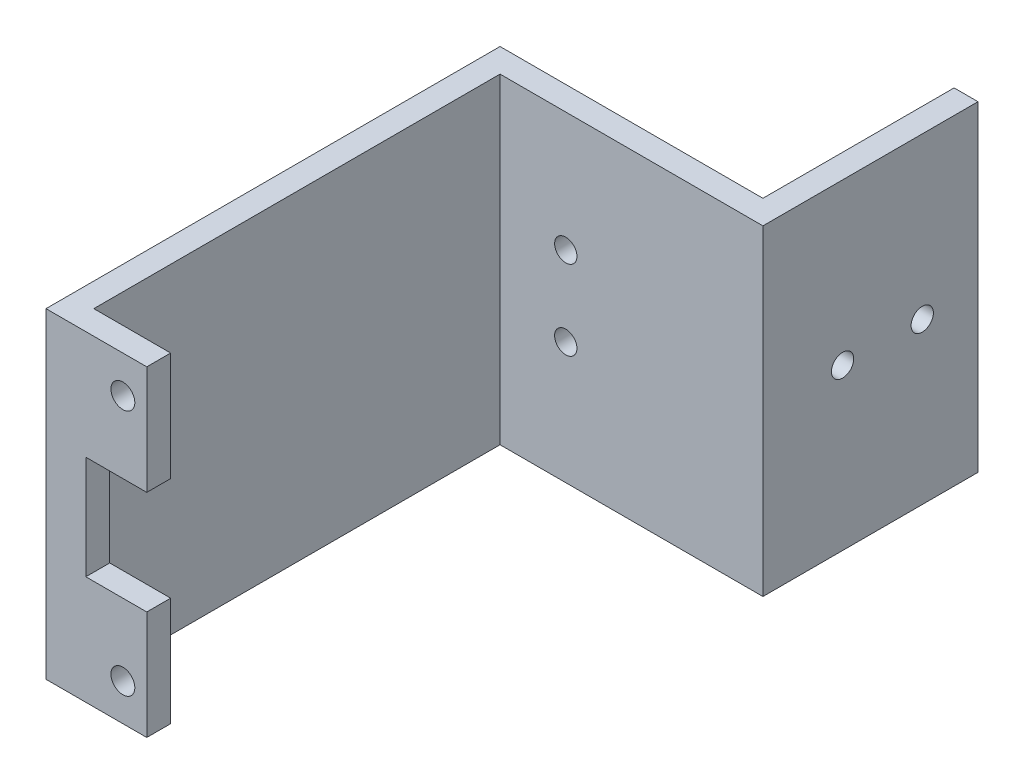
SolidWorks part; units mm, degrees
ref_plane "Front Plane" through (0, 0, 0) normal (0, 0, 1) x (1, 0, 0)
ref_plane "Top Plane" through (0, 0, 0) normal (0, 1, 0) x (1, 0, 0)
ref_plane "Right Plane" through (0, 0, 0) normal (1, 0, 0) x (0, 0, -1)
sketch "Sketch1" plane through (0, 0, 0) normal (0, 0, 1) x (1, 0, 0)
  line L0 (-28.851, -13) -> (-28.851, -20.15)
  line L1 (-28.851, -20.15) -> (-33.0868, -20.15)
  line L2 (-33.0868, -20.15) -> (-36.501, -16.7358)
  line L3 (-36.501, -16.7358) -> (-36.501, 16.7358)
  line L4 (-36.501, 16.7358) -> (-33.0868, 20.15)
  line L5 (-33.0868, 20.15) -> (-28.851, 20.15)
  line L6 (0.3848, 20.15) -> (-33.0868, 20.15) construction
  line L7 (-28.851, 20.15) -> (-28.851, 6.5)
  line L8 (-28.851, 6.5) -> (-36.501, 6.5)
  line L9 (-28.851, -13) -> (-28.851, -6.5)
  line L10 (-28.851, -6.5) -> (-36.501, -6.5)
  line L11 (-36.501, -6.5) -> (-31.501, -6.5) construction
  line L13 (-36.501, 6.5) -> (-31.501, 6.5) construction
  line L14 (-33.0868, -20.15) -> (-36.501, -20.15)
  line L15 (-36.501, -20.15) -> (-36.501, 20.15)
  line L16 (-36.501, 20.15) -> (-33.0868, 20.15)
  line L18 (-36.501, -20.15) -> (-41.501, -20.15)
  line L19 (-36.501, -20.15) -> (-36.501, 20.15)
  line L20 (-36.501, 20.15) -> (-41.501, 20.15)
  line L21 (-41.501, -20.15) -> (-41.501, 20.15)
  line L22 (-36.501, -20.15) -> (-41.501, 20.15) construction
  line L23 (-36.501, 20.15) -> (-41.501, -20.15) construction
  circle A0 centre (-31.851, -15.5) radius 1.5
  circle A1 centre (-31.851, 15.5) radius 1.5
  point P33 (-39.001, 0)
  dimension "D1" = 5
extrude "Boss-Extrude1" add sketch "Sketch1" along normal blind 3 contours L9 L10 L3 L2 L1 L0 A0 | L8 L7 L5 L4 L3 A1 | L15 L14 L2 | L16 L15 L4 | L21 L18 L15 L3 L20
sketch "Sketch2" plane through (-41.501, 0, 0) normal (1, 0, 0) x (0, 0, -1)
  line L1 (-3, -20.15) -> (51, -20.15)
  line L3 (-3, 20.15) -> (51, 20.15)
  line L4 (51, -20.15) -> (51, 20.15)
  line L5 (-3, -20.15) -> (51, 20.15) construction
  line L6 (-3, 20.15) -> (51, -20.15) construction
  line L7 (51, -20.15) -> (-49, -20.15)
  line L8 (51, -20.15) -> (51, 20.15)
  line L11 (-3, -20.15) -> (-3, 20.15) construction
  line L13 (0, -20.15) -> (-3, -20.15) construction
  line L14 (0, 20.15) -> (-3, 20.15) construction
  line L16 (51, -20.15) -> (49, -20.15)
  line L17 (51, -20.15) -> (51, 20.15)
  line L18 (51, 20.15) -> (49, 20.15)
  line L19 (49, -20.15) -> (49, 20.15)
  line L20 (51, -20.15) -> (49, 20.15) construction
  line L21 (51, 20.15) -> (49, -20.15) construction
  point P4 (24, 0)
  point P13 (-1.5, -20.15)
  point P16 (50, 0)
  dimension "D1" = 54
  dimension "D2" = 54
  dimension "D3" = 2
extrude "Boss-Extrude2" add sketch "Sketch2" along normal blind 3
sketch "Sketch3" plane through (0, 0, -51) normal (0, 0, -1) x (-1, 0, 0)
  line L0 (38.501, -20.15) -> (41.501, -20.15) construction
  line L5 (41.501, 20.15) -> (8.501, 20.15)
  line L6 (41.501, 20.15) -> (41.501, -20.15)
  line L8 (41.501, -20.15) -> (8.501, -20.15)
  line L9 (8.501, 20.15) -> (8.501, -20.15)
  line L10 (41.501, 20.15) -> (8.501, -20.15) construction
  line L11 (41.501, -20.15) -> (8.501, 20.15) construction
  line L12 (38.501, -20.15) -> (38.501, 20.15) construction
  circle A2 centre (30.251, 5.15) radius 1.4
  circle A3 centre (30.251, -4.85) radius 1.4
  point P4 (25.001, 0)
  point P14 (0, 0)
  point P19 (-11.0253, -70.8408)
  dimension "D4" = 11.25
  dimension "D5" = 15
  dimension "D6" = 2.8
  dimension "D7" = 2.8
  dimension "D1" = 0
  dimension "D2" = 30
  dimension "D3" = 10
extrude "Boss-Extrude3" add sketch "Sketch3" along normal blind 3
sketch "Sketch5" plane through (-8.501, 0, 0) normal (1, 0, 0) x (0, 0, -1)
  line L0 (54, 20.15) -> (-3, 20.15) construction
  line L1 (51, -20.15) -> (78, -20.15)
  line L2 (51, -20.15) -> (51, 20.15)
  line L3 (51, 20.15) -> (78, 20.15)
  line L4 (78, -20.15) -> (78, 20.15)
  line L5 (51, -20.15) -> (78, 20.15) construction
  line L6 (51, 20.15) -> (78, -20.15) construction
  line L8 (76, 11.25) -> (76, -11.25) construction
  circle A0 centre (71, 0) radius 1.4
  circle A1 centre (61, 0) radius 1.4
  point P4 (64.5, 0)
  point P16 (0, 0)
  dimension "D4" = 2.8
  dimension "D5" = 2.8
  dimension "D1" = 27
  dimension "D2" = 5
  dimension "D3" = 10
  dimension "D6" = 20.15
extrude "Boss-Extrude4" add sketch "Sketch5" along normal blind 3
